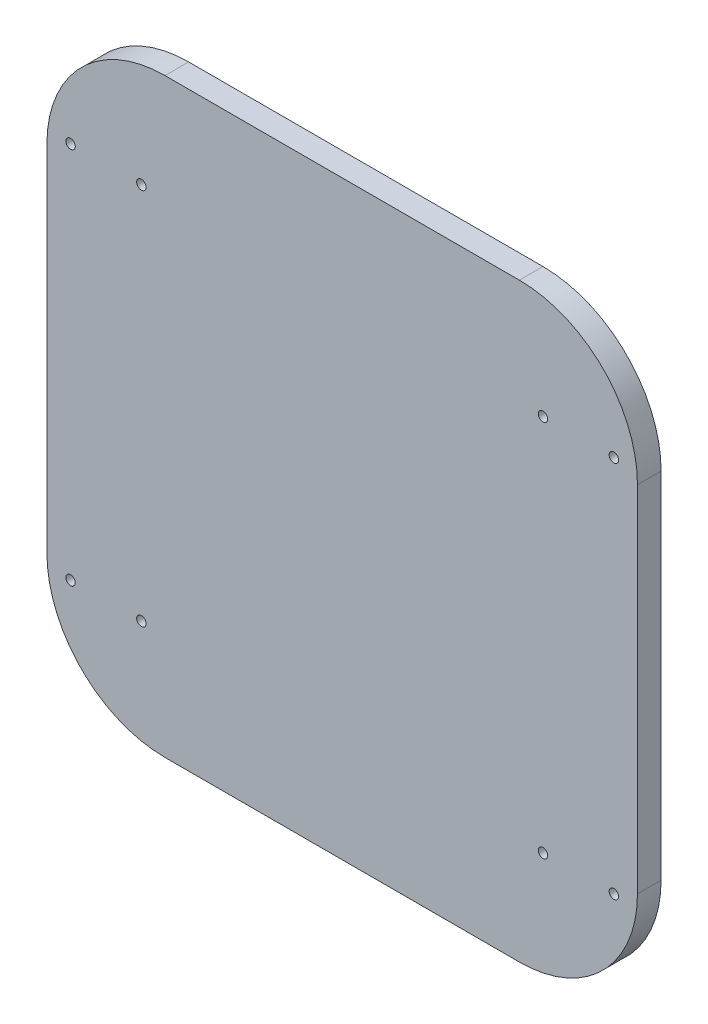
SolidWorks part; units mm, degrees
ref_plane "前视基准面" through (0, 0, 0) normal (0, 0, 1) x (1, 0, 0)
ref_plane "上视基准面" through (0, 0, 0) normal (0, 1, 0) x (1, 0, 0)
ref_plane "右视基准面" through (0, 0, 0) normal (1, 0, 0) x (0, 0, -1)
sketch "草图1" plane through (0, 0, 0) normal (0, 0, 1) x (1, 0, 0)
  line L0 (-75, -125) -> (75, -125)
  line L1 (-125, -75) -> (-125, 75)
  line L2 (125, -75) -> (125, 75)
  line L3 (-75, 125) -> (75, 125)
  line L4 (-125, -125) -> (125, 125) construction
  line L5 (125, -125) -> (-125, 125) construction
  arc A0 (75, -125) -> (125, -75) centre (75, -75) ccw
  arc A1 (-75, -125) -> (-125, -75) centre (-75, -75) cw
  arc A2 (125, 75) -> (75, 125) centre (75, 75) ccw
  arc A3 (-125, 75) -> (-75, 125) centre (-75, 75) cw
  point P1 (0, 0)
  dimension "D1" = 50
extrude "凸台-拉伸1" add sketch "草图1" along normal blind 10
sketch "草图2" plane through (0, 0, 10) normal (0, 0, 1) x (1, 0, 0)
  line L0 (0, 125) -> (0, -125) construction
  line L1 (75, 125) -> (-75, 125) construction
  line L2 (-75, -125) -> (75, -125) construction
  line L5 (-125, 0) -> (125, 0) construction
  line L6 (-125, 75) -> (-125, -75) construction
  line L7 (125, -75) -> (125, 75) construction
  circle A0 centre (115, 80) radius 2
  circle A1 centre (85, 80) radius 2
  circle A2 centre (115, -80) radius 2
  circle A3 centre (85, -80) radius 2
  circle A4 centre (-115, -80) radius 2
  circle A5 centre (-85, -80) radius 2
  circle A6 centre (-85, 80) radius 2
  circle A7 centre (-115, 80) radius 2
extrude "切除-拉伸1" cut sketch "草图2" against normal blind 8
sketch "草图3" plane through (0, 0, 0) normal (0, 0, -1) x (-1, 0, 0)
  line L0 (0, 125) -> (0, -126.8179) construction
  line L1 (-75, 125) -> (75, 125) construction
  line L4 (-20, 96.8464) -> (-20, -101.3353)
  line L5 (-50, 96.8464) -> (-50, -101.3353)
  line L6 (-70, 96.8464) -> (-70, -101.3353)
  line L7 (-100, 57.6136) -> (-100, -101.3353)
  line L8 (-85, 101.8464) -> (-75, 101.8464)
  line L9 (-95, -106.3353) -> (-75, -106.3353)
  line L10 (-100, 125) -> (-100, -135) construction
  line L11 (-70, 125) -> (-70, -135) construction
  line L12 (-50, 125) -> (-50, -135) construction
  line L13 (-20, 125) -> (-20, -135) construction
  line L14 (0, 125) -> (0, -135) construction
  line L15 (-45, 101.8464) -> (-25, 101.8464)
  line L16 (-45, -106.3353) -> (-25, -106.3353)
  line L17 (45, -106.3353) -> (25, -106.3353)
  line L18 (95, -106.3353) -> (75, -106.3353)
  line L19 (45, 101.8464) -> (25, 101.8464)
  line L20 (100, 57.6136) -> (100, -101.3353)
  line L21 (70, 96.8464) -> (70, -101.3353)
  line L22 (50, 96.8464) -> (50, -101.3353)
  line L23 (20, 96.8464) -> (20, -101.3353)
  line L24 (85, 101.8464) -> (75, 101.8464)
  arc A0 (-85, 101.8464) -> (-100, 57.6136) centre (13.471, 43.7937) ccw
  arc A1 (85, 101.8464) -> (100, 57.6136) centre (-13.471, 43.7937) cw
  arc A2 (70, 96.8464) -> (75, 101.8464) centre (75, 96.8464) cw
  arc A3 (95, -106.3353) -> (100, -101.3353) centre (95, -101.3353) ccw
  arc A4 (75, -106.3353) -> (70, -101.3353) centre (75, -101.3353) cw
  arc A5 (45, -106.3353) -> (50, -101.3353) centre (45, -101.3353) ccw
  arc A6 (25, -106.3353) -> (20, -101.3353) centre (25, -101.3353) cw
  arc A7 (50, 96.8464) -> (45, 101.8464) centre (45, 96.8464) ccw
  arc A8 (20, 96.8464) -> (25, 101.8464) centre (25, 96.8464) cw
  arc A9 (-20, 96.8464) -> (-25, 101.8464) centre (-25, 96.8464) ccw
  arc A10 (-50, 96.8464) -> (-45, 101.8464) centre (-45, 96.8464) cw
  arc A11 (-70, 96.8464) -> (-75, 101.8464) centre (-75, 96.8464) ccw
  arc A12 (-25, -106.3353) -> (-20, -101.3353) centre (-25, -101.3353) ccw
  arc A13 (-45, -106.3353) -> (-50, -101.3353) centre (-45, -101.3353) cw
  arc A14 (-75, -106.3353) -> (-70, -101.3353) centre (-75, -101.3353) ccw
  arc A15 (-100, -101.3353) -> (-95, -106.3353) centre (-95, -101.3353) ccw
  point P35 (70, 101.8464)
  point P38 (100, -106.3353)
  point P41 (70, -106.3353)
  point P44 (50, -106.3353)
  point P47 (20, -106.3353)
  point P50 (50, 101.8464)
  point P53 (20, 101.8464)
  point P56 (-20, 101.8464)
  point P59 (-50, 101.8464)
  point P62 (-70, 101.8464)
  point P65 (-20, -106.3353)
  point P68 (-50, -106.3353)
  point P71 (-70, -106.3353)
  point P74 (-100, -106.3353)
  dimension "D5" = 5
  dimension "D1" = 20
  dimension "D2" = 30
  dimension "D3" = 20
  dimension "D4" = 30
extrude "凸台-拉伸2" add sketch "草图3" along normal blind 10
